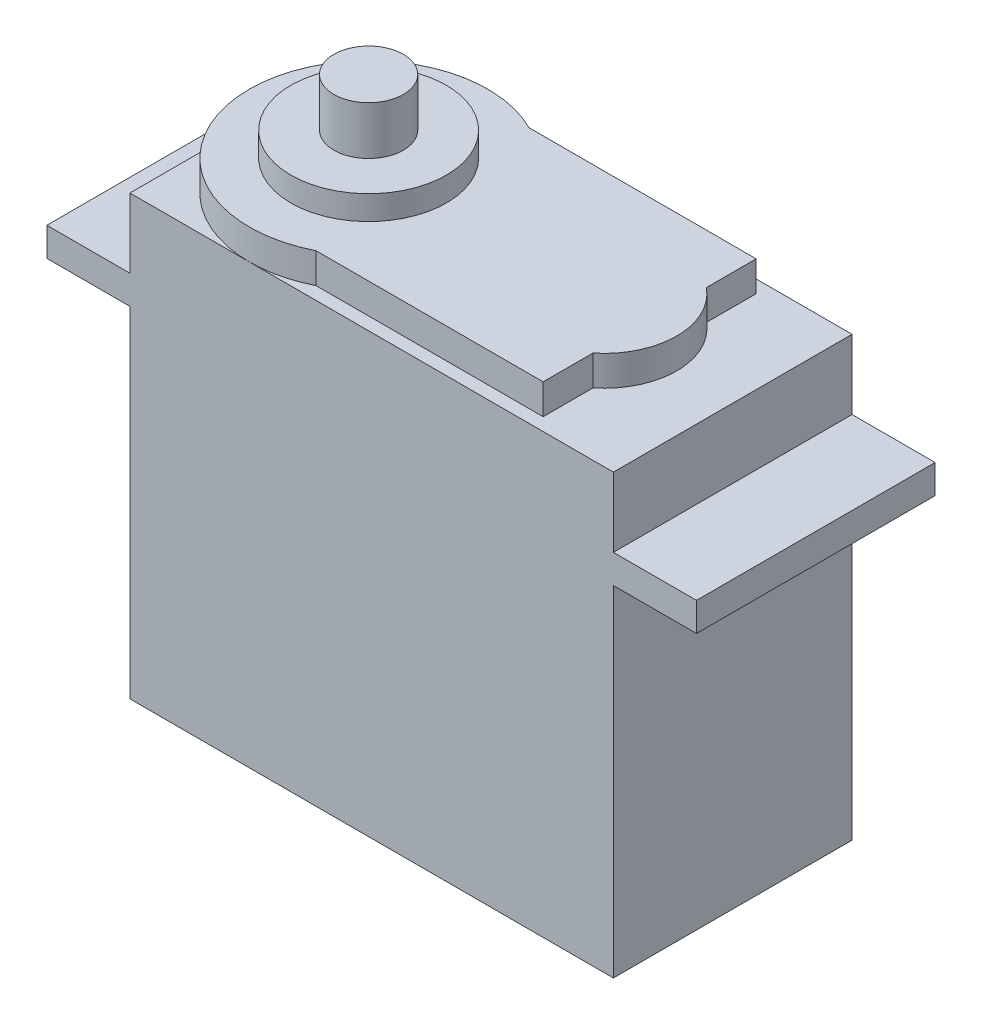
SolidWorks part; units mm, degrees
ref_plane "Front Plane" through (0, 0, 0) normal (0, 0, 1) x (1, 0, 0)
ref_plane "Top Plane" through (0, 0, 0) normal (0, 1, 0) x (1, 0, 0)
ref_plane "Right Plane" through (0, 0, 0) normal (1, 0, 0) x (0, 0, -1)
sketch "Sketch1" plane through (0, 0, 0) normal (0, 0, 1) x (1, 0, 0)
  line L0 (20.32, 36.83) -> (20.32, 0) construction
  line L1 (0, 0) -> (40.64, 0)
  line L2 (0, 0) -> (0, 28.575)
  line L3 (0, 36.83) -> (40.64, 36.83)
  line L4 (40.64, 0) -> (40.64, 28.575)
  line L5 (40.64, 30.988) -> (47.625, 30.988)
  line L7 (40.64, 28.575) -> (47.625, 28.575)
  line L8 (47.625, 30.988) -> (47.625, 28.575)
  line L9 (0, 28.575) -> (-6.985, 28.575)
  line L10 (-6.985, 30.988) -> (-6.985, 28.575)
  line L11 (0, 30.988) -> (-6.985, 30.988)
  line L12 (0, 30.988) -> (0, 36.83)
  line L13 (40.64, 30.988) -> (40.64, 36.83)
  dimension "D1" = 40.64
  dimension "D2" = 36.83
  dimension "D3" = 28.575
  dimension "D4" = 2.413
  dimension "D5" = 6.985
extrude "Boss-Extrude1" add sketch "Sketch1" along normal blind 20.066
ref_plane "Plane1" through (0, 36.83, 0) normal (0, 1, 0) x (1, 0, 0)
sketch "Sketch2" plane through (0, 36.83, 0) normal (0, 1, 0) x (1, 0, 0)
  line L1 (14.5602, -1.0795) -> (33.655, -1.0795)
  line L3 (14.5602, -18.9865) -> (33.655, -18.9865)
  line L4 (40.64, 0) -> (0, 0)
  line L5 (0, 0) -> (0, -20.066)
  line L6 (0, -20.066) -> (40.64, -20.066)
  line L7 (40.64, -20.066) -> (40.64, 0)
  line L8 (40.64, 0) -> (0, 0) construction
  line L9 (0, 0) -> (0, -20.066) construction
  line L10 (0, -20.066) -> (40.64, -20.066) construction
  line L11 (40.64, -20.066) -> (40.64, 0) construction
  line L12 (33.655, -1.0795) -> (33.655, -5.2705)
  line L13 (35.941, -10.033) -> (33.655, -10.033) construction
  line L14 (33.655, -14.7955) -> (33.655, -18.9865)
  arc A0 (14.5602, -1.0795) -> (14.5602, -18.9865) centre (10.033, -10.033) ccw
  arc A1 (33.655, -5.2705) -> (33.655, -14.7955) centre (29.8371, -10.033) cw
  point P16 (0, 0)
  dimension "D2" = 17.907
  dimension "D3" = 6.985
  dimension "D4" = 9.525
  dimension "D5" = 2.286
  dimension "D1" = 0
extrude "Boss-Extrude2" add sketch "Sketch2" along normal blind 2.54
sketch "Sketch3" plane through (0, 39.37, 0) normal (0, 1, 0) x (1, 0, 0)
  arc A0 (10.033, 0) -> (0, -10.033) centre (10.033, -10.033) ccw construction
  arc A1 (10.033, 0) -> (0, -10.033) centre (10.033, -10.033) ccw construction
  circle A2 centre (10.033, -10.033) radius 6.5405
  dimension "D1" = 13.081
extrude "Boss-Extrude3" add sketch "Sketch3" along normal blind 2.032
sketch "Sketch4" plane through (0, 41.402, 0) normal (0, 1, 0) x (1, 0, 0)
  circle A0 centre (10.033, -10.033) radius 2.921
  circle A1 centre (10.033, -10.033) radius 6.5405
  circle A2 centre (10.033, -10.033) radius 6.5405 construction
  dimension "D2" = 5.842
  dimension "D1" = 0
extrude "Boss-Extrude4" add sketch "Sketch4" along normal blind 4.064
